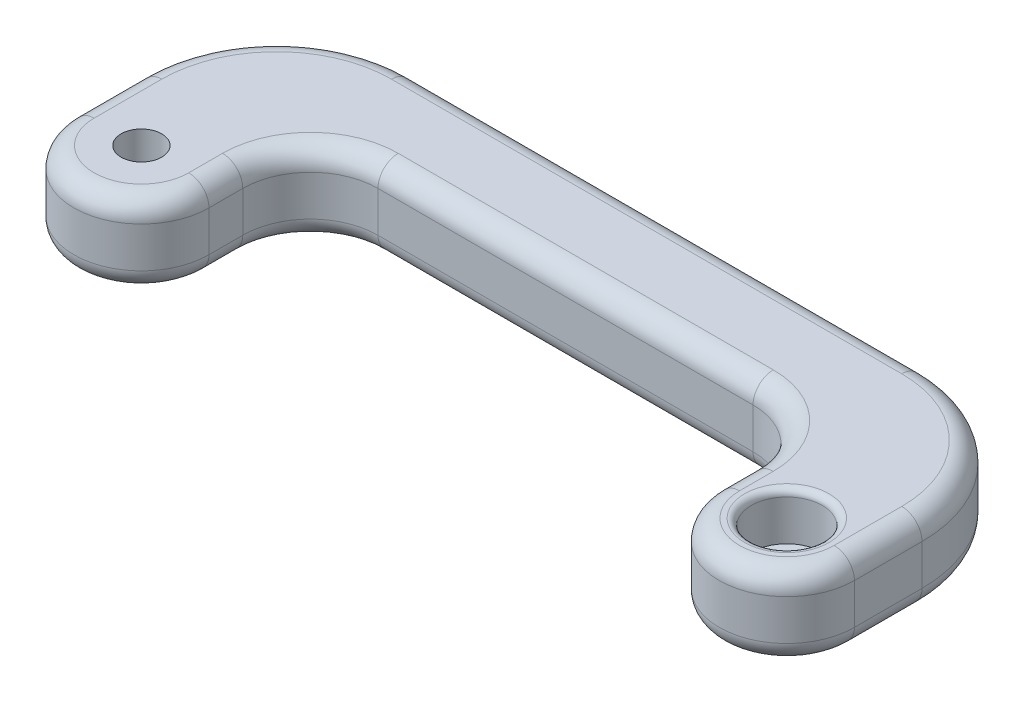
SolidWorks part; units mm, degrees
ref_plane "Front Plane" through (0, 0, 0) normal (0, 0, 1) x (1, 0, 0)
ref_plane "Top Plane" through (0, 0, 0) normal (0, 1, 0) x (1, 0, 0)
ref_plane "Right Plane" through (0, 0, 0) normal (1, 0, 0) x (0, 0, -1)
sketch "Sketch7" plane through (0, 0, 0) normal (0, 1, 0) x (1, 0, 0)
  line L2 (-105.5, 0) -> (-105.5, 30)
  line L3 (-85.5, 0) -> (-85.5, 15)
  line L4 (-105.5, 30) -> (-85.5, 30)
  line L6 (-85.5, 30) -> (10, 30)
  line L7 (-85.5, 15) -> (-10, 15)
  line L10 (10, 0) -> (10, 30.0013)
  line L11 (-10, 0) -> (-10, 15)
  line L12 (10, 30.0013) -> (-10, 30.0013)
  line L13 (-10, 30) -> (-10, 30.0013)
  arc A0 (-10, 0) -> (10, 0) centre (0, 0) ccw
  arc A1 (-105.5, 0) -> (-85.5, 0) centre (-95.5, 0) ccw
  circle A2 centre (-95.5, 0) radius 5
extrude "Boss-Extrude5" add sketch "Sketch7" along normal blind 12 contours L2 A1 L3 L7 L11 A0 L10 L6 L4 A2
sketch "Sketch8" plane through (0, 12, 0) normal (0, 1, 0) x (1, 0, 0)
  circle A0 centre (0, 0) radius 6
fillet "Fillet2" radius 20 2 edges at (10, 6, -30) (-105.5, 6, -30)
fillet "Fillet3" radius 10 2 edges at (-10, 6, -15) (-85.5, 6, -15)
fillet "Fillet5" radius 3 24 edges at (-47.75, 12, -30) (4.1421, 12, -24.1421) (10, 12, -5) (0, 12, 10) (-10, 12, -2.5) (-12.9289, 12, -12.0711) (-47.75, 12, -15) (-82.5711, 12, -12.0711) (-85.5, 12, -2.5) (-95.5, 12, 10) (-105.5, 12, -5) (-105.5, 0, -5) (-95.5, 0, 10) (-85.5, 0, -2.5) (-82.5711, 0, -12.0711) (-47.75, 0, -15) (-12.9289, 0, -12.0711) (-10, 0, -2.5) (0, 0, 10) (10, 0, -5) (4.1421, 0, -24.1421) (-47.75, 0, -30) (-99.6421, 12, -24.1421) (-99.6421, 0, -24.1421)
sketch "Sketch10" plane through (0, 12, 0) normal (0, 1, 0) x (1, 0, 0)
  circle A0 centre (-95.5, 0) radius 5.1
sketch "Sketch11" plane through (0, 0, 0) normal (0, -1, 0) x (1, 0, 0)
  circle A0 centre (-95.5, 0) radius 5.25
  circle A1 centre (0, 0) radius 5.25
extrude "Cut-Extrude1" cut sketch "Sketch11" against normal blind 36
fillet "Fillet6" radius 1 4 edges at (-95.5, 12, 5.25) (0, 12, 5.25) (0, 0, -5.25) (-95.5, 0, -5.25)
sketch "Sketch12" plane through (0, 12, 0) normal (0, 1, 0) x (1, 0, 0)
  circle A0 centre (-95.5, 0) radius 6.25
  circle A1 centre (-95.5, 0) radius 3
extrude "Boss-Extrude6" add sketch "Sketch12" against normal blind 5
sketch "Sketch13" plane through (0, 0, 0) normal (0, -1, 0) x (1, 0, 0)
  circle A0 centre (0, 0) radius 6.25
  circle A1 centre (0, 0) radius 3
extrude "Boss-Extrude7" add sketch "Sketch13" against normal blind 5
